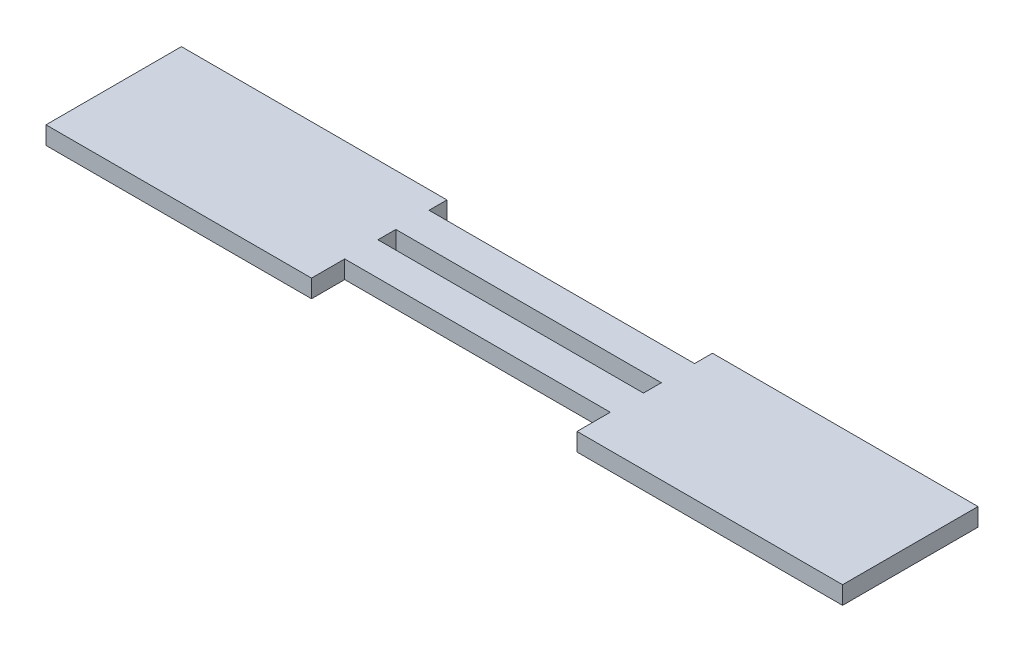
SolidWorks part; units mm, degrees
ref_plane "Front Plane" through (0, 0, 0) normal (0, 0, 1) x (1, 0, 0)
ref_plane "Top Plane" through (0, 0, 0) normal (0, 1, 0) x (1, 0, 0)
ref_plane "Right Plane" through (0, 0, 0) normal (1, 0, 0) x (0, 0, -1)
sketch "Sketch1" plane through (0, 0, 0) normal (0, 1, 0) x (1, 0, 0)
  line L0 (-20, 1.7909) -> (20, 1.7909)
  line L1 (-60, 4.4909) -> (-20, 4.4909)
  line L2 (-60, 4.4909) -> (-60, -3.2091)
  line L3 (-60, -15.9091) -> (-20, -15.9091)
  line L4 (60, 4.4909) -> (60, -3.2091)
  line L7 (-20, -3.2091) -> (20, -3.2091)
  line L9 (20, 4.4909) -> (60, 4.4909)
  line L10 (-20, -10.9091) -> (-20, -15.9091)
  line L12 (-20, -10.9091) -> (20, -10.9091)
  line L13 (20, -5.9091) -> (-20, -5.9091)
  line L14 (-20, 4.4909) -> (-20, 1.7909)
  line L15 (20, 4.4909) -> (20, 1.7909)
  line L16 (20, -3.2091) -> (20, -5.9091)
  line L17 (-20, -3.2091) -> (-20, -5.9091)
  line L19 (20, -10.9091) -> (20, -15.9091)
  line L20 (-60, -5.9091) -> (-60, -15.9091)
  line L21 (60, -5.9091) -> (60, -15.9091)
  line L22 (20, -15.9091) -> (60, -15.9091)
  line L23 (60, -3.2091) -> (60, -5.9091)
  line L24 (-60, -3.2091) -> (-60, -5.9091)
  point P0 (0, 0)
  dimension "D1" = 120
  dimension "D2" = 20.4
  dimension "D3" = 2.7
extrude "Boss-Extrude1" add sketch "Sketch1" along normal blind 2.7
